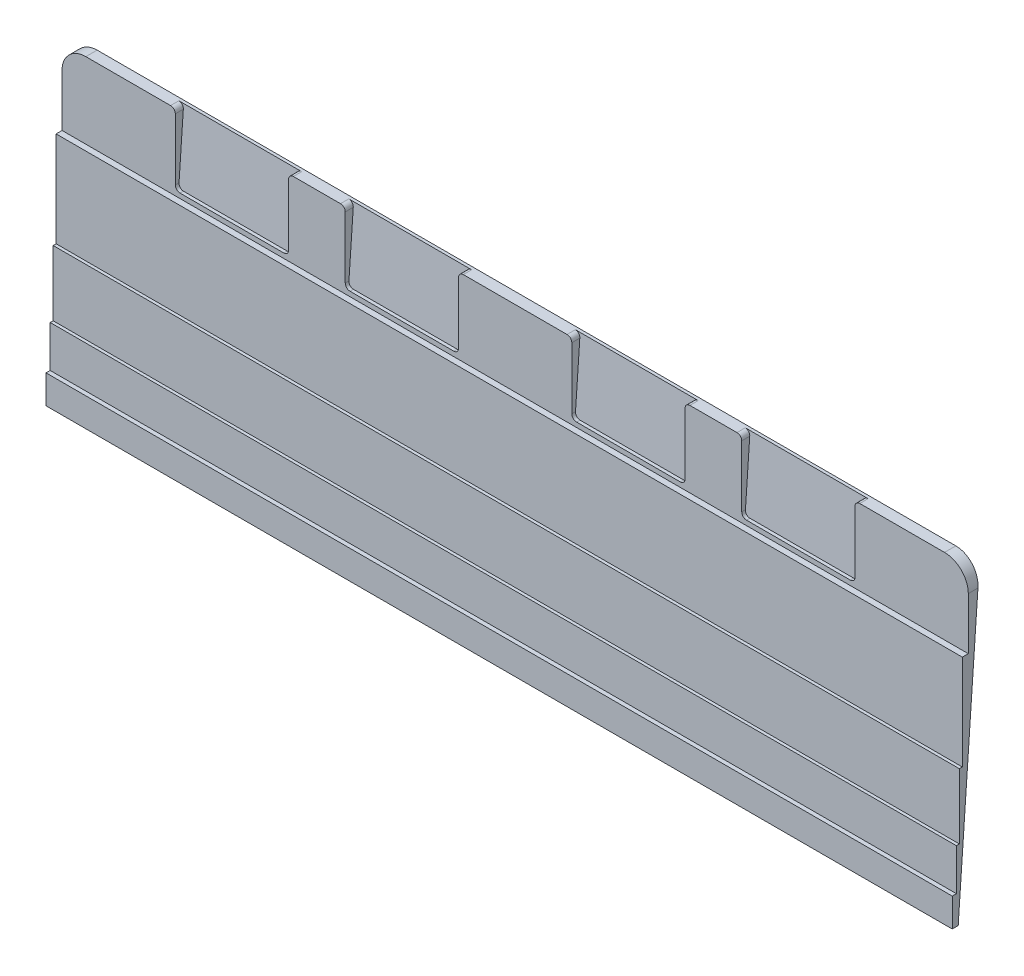
SolidWorks part; units mm, degrees
material "Glass"
ref_plane "Front Plane" through (0, 0, 0) normal (0, 0, 1) x (1, 0, 0)
ref_plane "Top Plane" through (0, 0, 0) normal (0, 1, 0) x (1, 0, 0)
ref_plane "Right Plane" through (0, 0, 0) normal (1, 0, 0) x (0, 0, -1)
ref_plane "Plane1" through (-149.225, 0, 0) normal (-1, 0, 0) x (0, 0, 1)
ref_plane "Plane2" through (155.5753, 0, 0) normal (1, 0, 0) x (0, 0, -1)
sketch "Sketch1" plane through (-149.225, 0, 0) normal (-1, 0, 0) x (0, 0, 1)
  line L1 (-2, -64.0237) -> (-3.3962, -64.0237)
  line L2 (-4, 84.0184) -> (-4, -73.6248) construction
  line L3 (-4, -73.6248) -> (-11.2027, 29.3782)
  line L4 (-3.3962, -64.0237) -> (-3.3962, -50.0488)
  line L5 (14.1038, -73.6248) -> (-62.5482, -73.6248) construction
  line L6 (-4, -73.6248) -> (-15.0962, 85.0583) construction
  line L7 (-3.3962, -50.0488) -> (-4.3962, -50.0488)
  line L9 (-4.3962, -50.0488) -> (-4.3962, -28.1263)
  line L10 (-4.3962, -28.1263) -> (-5.3962, -28.1263)
  line L11 (-5.3962, 3.8737) -> (-7.3962, 3.8737) construction
  line L14 (-2, -73.6248) -> (-4, -73.6248)
  line L16 (-2, -73.6248) -> (-2, -64.0237)
  line L17 (-5.3962, -28.1263) -> (-5.3962, 3.8737)
  line L19 (-5.3962, 3.8737) -> (-7.3962, 3.8737)
  line L20 (-7.3962, 3.8737) -> (-7.3962, 29.3782)
  line L21 (-7.3962, 29.3782) -> (-11.2027, 29.3782)
  line L22 (-4.3962, -28.1263) -> (-5.3962, -28.1263) construction
  line L24 (-3.3962, -50.0488) -> (-4.3962, -50.0488) construction
  line L25 (-2, -64.0237) -> (-3.3962, -64.0237) construction
  point P6 (0, 0)
  point P18 (0, 0)
  point P30 (0, 0)
  point P33 (0, 0)
  point P35 (0, 0)
  point P37 (0, 0)
  dimension "D1" = 73.6248
  dimension "D2" = 2
  dimension "D3" = 4
extrude "Boss-Extrude1" add sketch "Sketch1" against normal up to surface (304.8003 mm away) up to plane "Plane2"
fillet "Fillet1" radius 8 2 edges at (155.5753, 29.3782, -9.2994) (-149.225, 29.3782, -9.2994)
sketch "Sketch2" plane through (0, 0, -7.3962) normal (0, 0, 1) x (1, 0, 0)
  line L0 (3.1753, 121.2498) -> (3.1753, -113.2057) construction
  line L1 (10.1748, 54.6246) -> (-3.8242, 54.6246) construction
  line L2 (60.3261, 5.4737) -> (22.2253, 5.4737)
  line L3 (-104.1252, 35.5747) -> (-118.1245, 35.5747) construction
  line L12 (-111.1249, 5.4737) -> (-111.1249, 29.3782)
  line L13 (-111.1249, 29.3782) -> (-73.0249, 29.3782)
  line L14 (-73.0249, 29.3782) -> (-73.0249, 5.4737)
  line L15 (-66.0252, 35.5747) -> (-80.0245, 35.5747) construction
  line L16 (-53.9756, 5.4737) -> (-53.9756, 29.3782)
  line L17 (-53.9756, 29.3782) -> (-15.8747, 29.3782)
  line L18 (-15.8747, 29.3782) -> (-15.8747, 5.4737)
  line L19 (-46.9752, 35.5747) -> (-60.9759, 35.5747) construction
  line L20 (-8.8752, 35.5747) -> (-22.8742, 35.5747) construction
  line L21 (-111.1249, 5.4737) -> (-73.0249, 5.4737)
  line L22 (-53.9756, 5.4737) -> (-15.8747, 5.4737)
  line L23 (117.4754, 5.4737) -> (79.3754, 5.4737)
  line L24 (22.2253, 29.3782) -> (22.2253, 5.4737)
  line L25 (60.3261, 29.3782) -> (22.2253, 29.3782)
  line L26 (60.3261, 5.4737) -> (60.3261, 29.3782)
  line L27 (79.3754, 29.3782) -> (79.3754, 5.4737)
  line L28 (117.4754, 29.3782) -> (79.3754, 29.3782)
  line L29 (117.4754, 5.4737) -> (117.4754, 29.3782)
  line L31 (147.5753, 29.3782) -> (-141.225, 29.3782) construction
  line L33 (155.5753, 3.8737) -> (-149.225, 3.8737) construction
  point P12 (3.1753, 54.6246)
  point P24 (-111.1249, 35.5747)
  point P27 (-73.0249, 35.5747)
  point P30 (-53.9756, 35.5747)
  point P33 (-15.8747, 35.5747)
  dimension "D1" = 1.6
extrude "Cut-Extrude1" cut sketch "Sketch2" against normal offset from surface (2.804 mm away) 1
fillet "Fillet2" radius 1.6 8 edges at (-15.8747, 5.4737, -7.9624) (-53.9756, 5.4737, -7.9624) (-111.1249, 5.4737, -7.9624) (-73.0249, 5.4737, -7.9624) (79.3754, 5.4737, -7.9624) (117.4754, 5.4737, -7.9624) (60.3261, 5.4737, -7.9624) (22.2253, 5.4737, -7.9624)
fillet "Fillet3" radius 1.6 8 edges at (117.4754, 29.3782, -8.7982) (60.3261, 29.3782, -8.7982) (79.3754, 29.3782, -8.7982) (22.2253, 29.3782, -8.7982) (-15.8747, 29.3782, -8.7982) (-53.9756, 29.3782, -8.7982) (-73.0249, 29.3782, -8.7982) (-111.1249, 29.3782, -8.7982)
